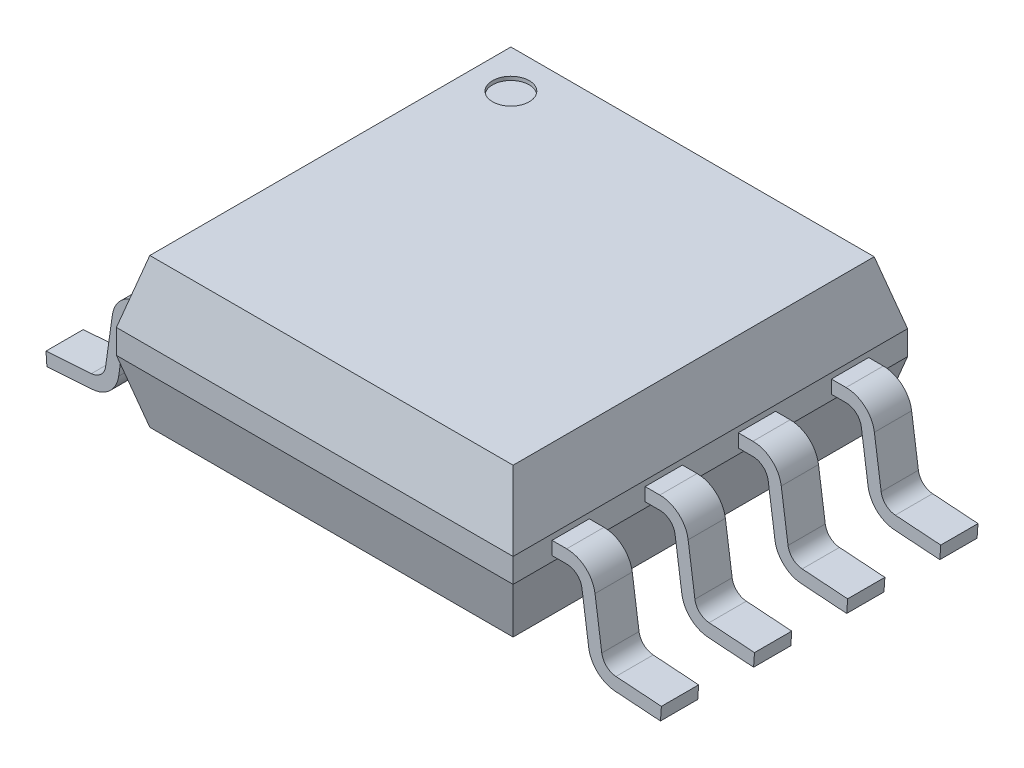
SolidWorks part; units mm, degrees
ref_plane "FRONT" through (0, 0, 0) normal (0, 0, 1) x (1, 0, 0)
ref_plane "TOP" through (0, 0, 0) normal (0, 1, 0) x (1, 0, 0)
ref_plane "RIGHT" through (0, 0, 0) normal (1, 0, 0) x (0, 0, -1)
sketch "Sketch1" plane through (0, 0, 0) normal (0, 1, 0) x (1, 0, 0)
  line L0 (0, 0) -> (0, 2.69) construction
  line L1 (-2.705, 2.69) -> (2.705, 2.69)
  line L2 (-2.705, 2.69) -> (-2.705, -2.69)
  line L3 (-2.705, -2.69) -> (2.705, -2.69)
  line L4 (2.705, 2.69) -> (2.705, -2.69)
  line L5 (0, 0) -> (2.705, 0) construction
  dimension "D1" = 5.41
  dimension "D2" = 5.38
extrude "Base-Extrude" add sketch "Sketch1" against normal blind 2.03
ref_plane "LEG PLANE" through (0, 0, -1.905) normal (0, 0, 1) x (1, 0, 0)
sketch "Sketch2" plane through (0, 0, -1.905) normal (0, 0, 1) x (1, 0, 0)
  line L0 (-2.705, -1.015) -> (-2.905, -1.015)
  line L1 (-2.705, -2.03) -> (-2.705, 0) construction
  line L2 (-3.2021, -1.2732) -> (-3.2943, -1.9292)
  line L3 (-3.5704, -2.1867) -> (-4.19, -2.23)
  line L5 (0, 0) -> (0, 1.3276) construction
  line L6 (-2.705, -1.015) -> (-0.9713, -1.015) construction
  line L8 (-2.705, -2.03) -> (2.705, -2.03) construction
  arc A0 (-2.905, -1.015) -> (-3.2021, -1.2732) centre (-2.905, -1.315) ccw
  arc A1 (-3.5704, -2.1867) -> (-3.2943, -1.9292) centre (-3.5913, -1.8874) ccw
  dimension "D4" = 0.3
  dimension "D7" = 0.3
  dimension "D1" = 4
  dimension "D2" = 0.2
  dimension "D3" = 8.38
  dimension "D5" = 8
  dimension "D6" = 0.2
extrude "PIN 1" add sketch "Sketch2" along normal mid plane 0.508 thin thin type mid plane wall 0.18
mirror "PIN 8" about plane through (0, 0, 0) normal (1, 0, 0) of "PIN 1"
pattern_linear "LPattern1" count 4 spacing 1.27 along (0, 0, 1) of "PIN 8", "PIN 1"
sketch "Sketch5" [suppressed] plane through (0, 0, -1.905) normal (0, 0, 1) x (1, 0, 0)
  line L0 (-2.705, -1.015) -> (-1.5058, -1.015) construction
  line L1 (-2.705, -2.03) -> (-2.705, 0) construction
  line L2 (-2.705, -1.015) -> (-2.725, -1.015)
  line L3 (-3.005, -1.295) -> (-3.005, -1.95)
  line L4 (-2.725, -2.23) -> (-1.8178, -2.23)
  line L5 (-2.705, -2.03) -> (2.705, -2.03) construction
  arc A0 (-2.725, -1.015) -> (-3.005, -1.295) centre (-2.725, -1.295) ccw
  arc A1 (-2.725, -2.23) -> (-3.005, -1.95) centre (-2.725, -1.95) cw
  dimension "D1" = 0.28
  dimension "D2" = 0.2
  dimension "D3" = 0.3
chamfer "TOP CHAMFER" distance 0.85 angle 15 4 edges at (0, 0, -2.69) (2.705, 0, 0) (0, 0, 2.69) (-2.705, 0, 0)
chamfer "BOTTOM CHAMFER" distance 0.85 angle 15 4 edges at (2.705, -2.03, 0) (0, -2.03, -2.69) (-2.705, -2.03, 0) (0, -2.03, 2.69)
sketch "Sketch3" plane through (0, 0, 0) normal (0, 1, 0) x (-1, 0, 0)
  line L0 (2.705, -2.69) -> (-2.705, -2.69) construction
  line L1 (2.705, 2.69) -> (2.705, -2.69) construction
  circle A0 centre (1.955, -1.94) radius 0.25
  dimension "D1" = 0.5
  dimension "D2" = 0.75
  dimension "D3" = 0.75
extrude "PIN1 HOL" cut sketch "Sketch3" against normal blind 0.05
